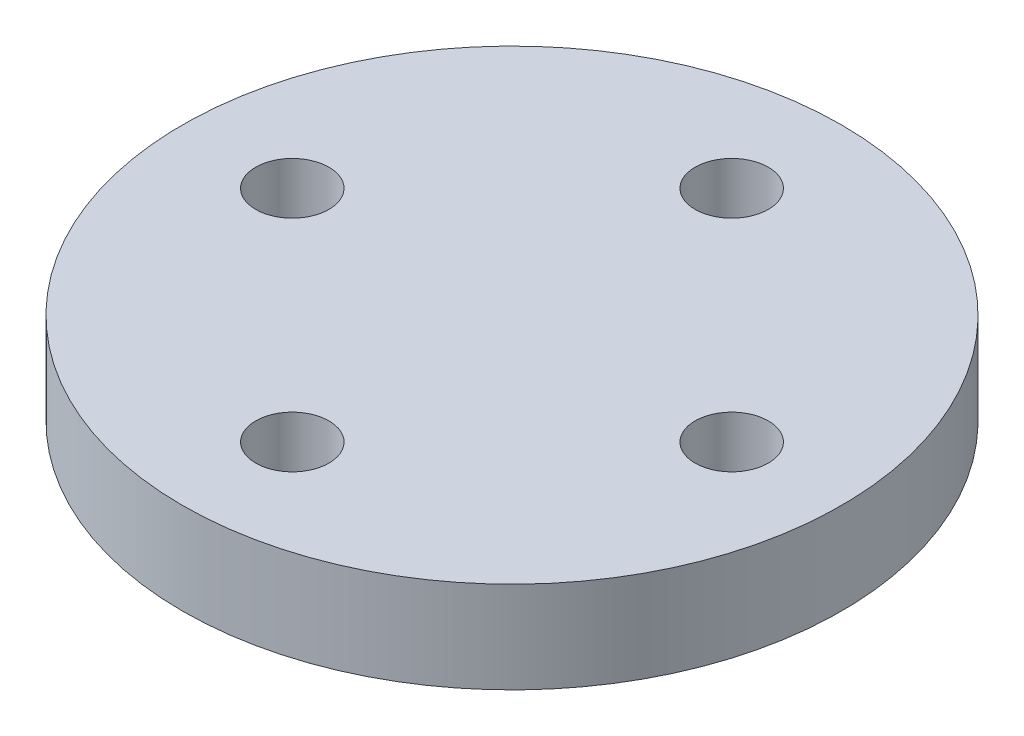
SolidWorks part; units mm, degrees
ref_plane "Front Plane" through (0, 0, 0) normal (0, 0, 1) x (1, 0, 0)
ref_plane "Top Plane" through (0, 0, 0) normal (0, 1, 0) x (1, 0, 0)
ref_plane "Right Plane" through (0, 0, 0) normal (1, 0, 0) x (0, 0, -1)
sketch "Sketch1" plane through (0, 0, 0) normal (0, 1, 0) x (1, 0, 0)
  line L0 (0, 0) -> (12, 0) construction
  line L1 (0, 0) -> (0, 12) construction
  circle A0 centre (0, 0) radius 12 construction
  circle A1 centre (0, 0) radius 18
  circle A2 centre (0, 12) radius 2
  circle A3 centre (0, 0) radius 18
  circle A4 centre (12, 0) radius 2
  circle A5 centre (0, 0) radius 18
  circle A6 centre (0, -12) radius 2
  circle A7 centre (0, 0) radius 18
  circle A8 centre (-12, 0) radius 2
  point P19 (0, 0)
  dimension "D1" = 24
  dimension "D2" = 36
  dimension "D3" = 4
  dimension "D4" = 90
  dimension "D5" = 4
extrude "Boss-Extrude1" add sketch "Sketch1" along normal blind 5 contours A1 A8 A6 A4 A2
